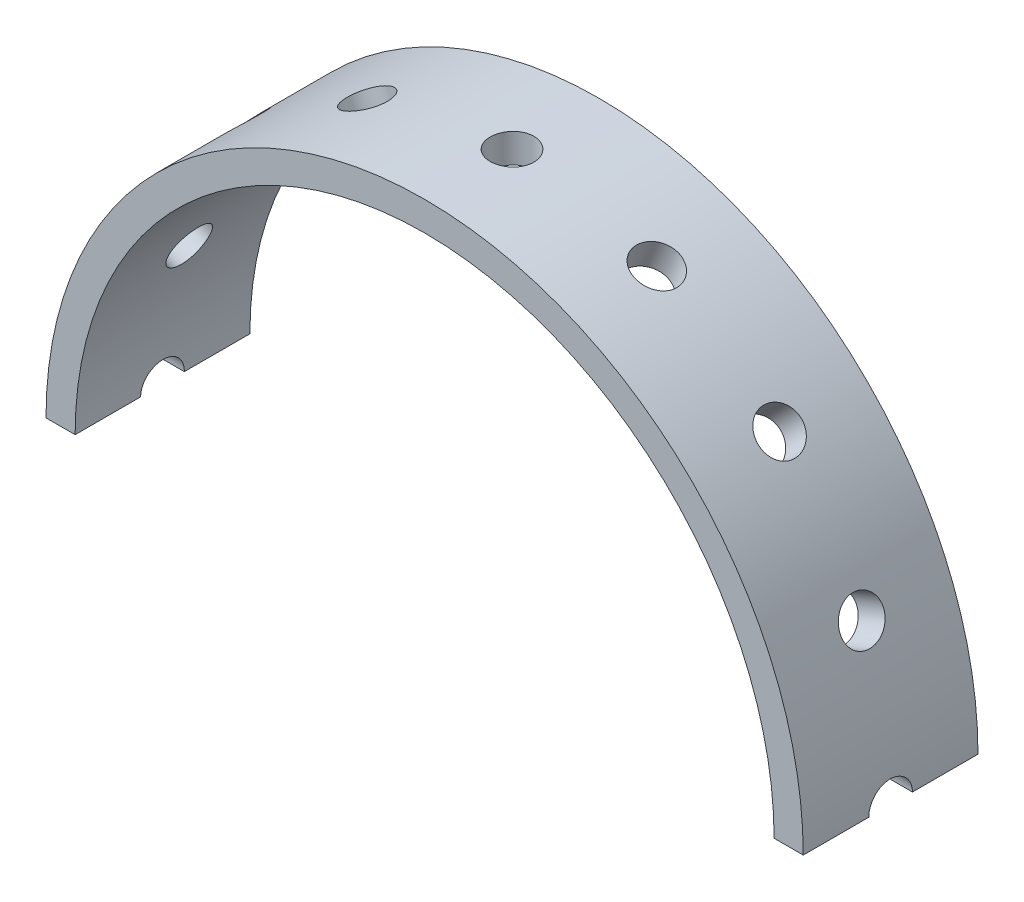
SolidWorks part; units mm, degrees
ref_plane "正面" through (0, 0, 0) normal (0, 0, 1) x (1, 0, 0)
ref_plane "平面" through (0, 0, 0) normal (0, 1, 0) x (1, 0, 0)
ref_plane "右側面" through (0, 0, 0) normal (1, 0, 0) x (0, 0, -1)
sketch "ｽｹｯﾁ1" plane through (0, 0, 0) normal (0, 0, 1) x (1, 0, 0)
  circle A0 centre (0, 0) radius 12
  circle A1 centre (0, 0) radius 13
  dimension "D1" = 24
  dimension "D2" = 26
extrude "ﾎﾞｽ - 押し出し1" add sketch "ｽｹｯﾁ1" along normal blind 6
sketch "ｽｹｯﾁ2" plane through (0, 0, 0) normal (0, 1, 0) x (1, 0, 0)
  line L0 (13, 0) -> (-13, 0) construction
  circle A0 centre (0, -3) radius 0.75
  dimension "D1" = 1.5
  dimension "D2" = 3
extrude "ｶｯﾄ - 押し出し1" cut sketch "ｽｹｯﾁ2" against normal through all
pattern_circular "円形ﾊﾟﾀｰﾝ1" count 16 over 360 about axis through (0, 0, 0) along (0, 0, 1) of "ｶｯﾄ - 押し出し1"
sketch "ｽｹｯﾁ3" plane through (0, 0, 0) normal (0, 1, 0) x (1, 0, 0)
  line L1 (18.3993, -8.0013) -> (-18.3993, -8.0013)
  line L2 (18.3993, -8.0013) -> (18.3993, 3.9448)
  line L3 (18.3993, 3.9448) -> (-18.3993, 3.9448)
  line L4 (-18.3993, -8.0013) -> (-18.3993, 3.9448)
  line L5 (18.3993, -8.0013) -> (-18.3993, 3.9448) construction
  line L6 (18.3993, 3.9448) -> (-18.3993, -8.0013) construction
  point P0 (0, -2.0282)
extrude "ｶｯﾄ - 押し出し2" cut sketch "ｽｹｯﾁ3" against normal through all
